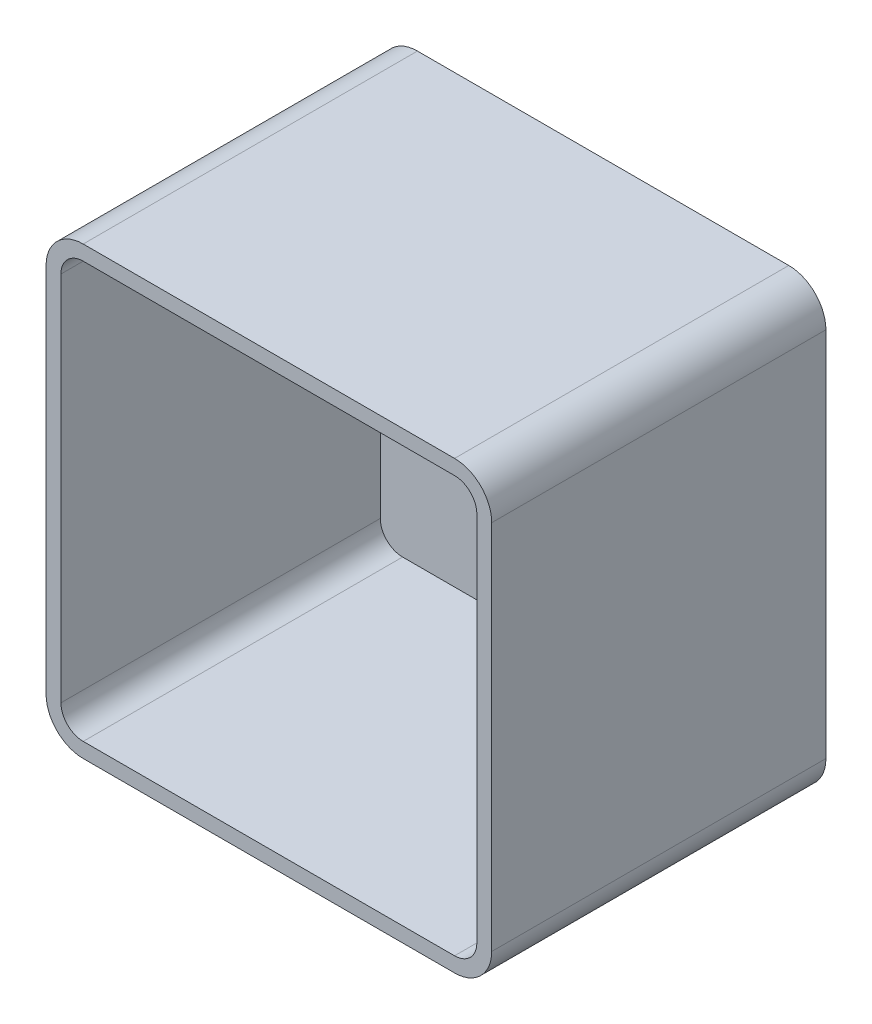
SolidWorks part; units mm, degrees
ref_plane "Front Plane" through (0, 0, 0) normal (0, 0, 1) x (1, 0, 0)
ref_plane "Top Plane" through (0, 0, 0) normal (0, 1, 0) x (1, 0, 0)
ref_plane "Right Plane" through (0, 0, 0) normal (1, 0, 0) x (0, 0, -1)
sketch "Sketch1" plane through (0, 0, 0) normal (0, 0, 1) x (1, 0, 0)
  line L1 (0, 0) -> (120, 0)
  line L2 (0, 0) -> (0, 120)
  line L3 (0, 120) -> (120, 120)
  line L4 (120, 0) -> (120, 120)
  dimension "D1" = 120
  dimension "D2" = 120
extrude "Boss-Extrude1" add sketch "Sketch1" along normal blind 90
fillet "Fillet1" radius 10 4 edges at (0, 0, 45) (120, 0, 45) (120, 120, 45) (0, 120, 45)
shell "Shell1" thickness 4
